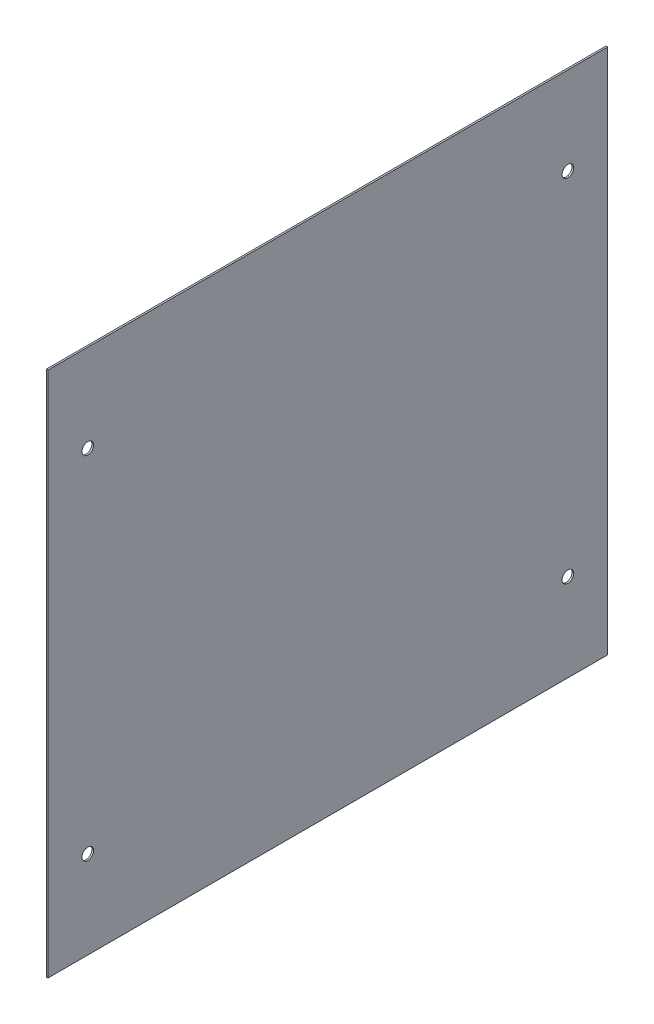
SolidWorks part; units mm, degrees
material "AISI 304"
ref_plane "Front Plane" through (0, 0, 0) normal (0, 0, 1) x (1, 0, 0)
ref_plane "Top Plane" through (0, 0, 0) normal (0, 1, 0) x (1, 0, 0)
ref_plane "Right Plane" through (0, 0, 0) normal (1, 0, 0) x (0, 0, -1)
sketch "Sketch1" plane through (0, 0, 0) normal (1, 0, 0) x (0, 0, -1)
  line L1 (0, 0) -> (338, 0)
  line L2 (0, 0) -> (0, 318)
  line L3 (0, 318) -> (338, 318)
  line L4 (338, 0) -> (338, 318)
  circle A0 centre (24, 265.06) radius 3.5
  circle A1 centre (314, 265.06) radius 3.5
  circle A2 centre (314, 52.94) radius 3.5
  circle A3 centre (24, 52.94) radius 3.5
  dimension "D3" = 7
  dimension "D1" = 318
  dimension "D2" = 338
  dimension "D4" = 52.94
  dimension "D5" = 52.94
  dimension "D6" = 24
  dimension "D7" = 24
extrude "Boss-Extrude1" add sketch "Sketch1" along normal blind 1
